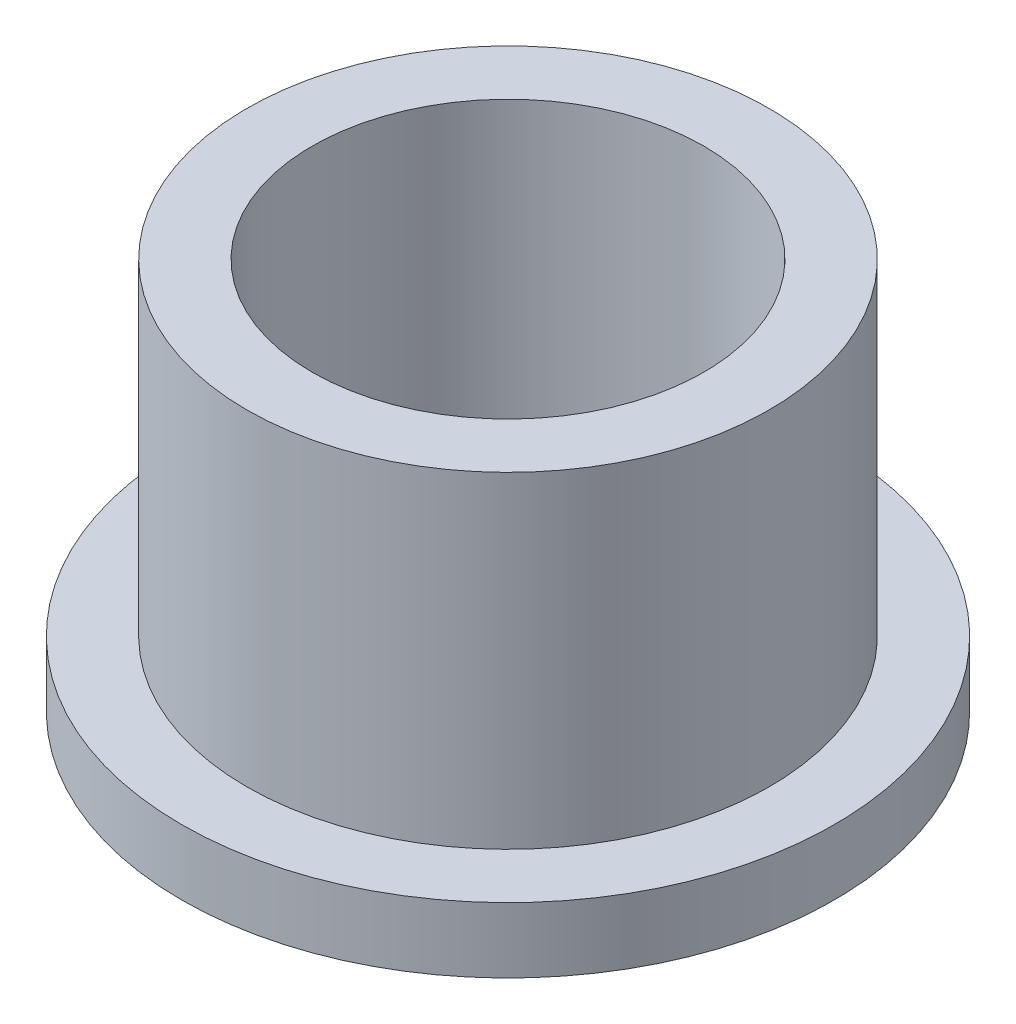
SolidWorks part; units mm, degrees
ref_plane "Front Plane" through (0, 0, 0) normal (0, 0, 1) x (1, 0, 0)
ref_plane "Top Plane" through (0, 0, 0) normal (0, 1, 0) x (1, 0, 0)
ref_plane "Right Plane" through (0, 0, 0) normal (1, 0, 0) x (0, 0, -1)
sketch "shaft" plane through (0, 0, 0) normal (0, 1, 0) x (1, 0, 0)
  circle A0 centre (0, 0) radius 4.7625
sketch "Flange" plane through (0, 0, 0) normal (0, 1, 0) x (1, 0, 0)
  circle A0 centre (0, 0) radius 7.9375
sketch "tube" plane through (0, 0, 0) normal (0, 1, 0) x (1, 0, 0)
  circle A0 centre (0, 0) radius 6.35
extrude "Boss-Extrude1" add sketch "tube" along normal blind 9.525
extrude "Boss-Extrude2" add sketch "Flange" along normal blind 1.5875 contours A0
extrude "Cut-Extrude1" cut sketch "shaft" along normal blind 9.5875
